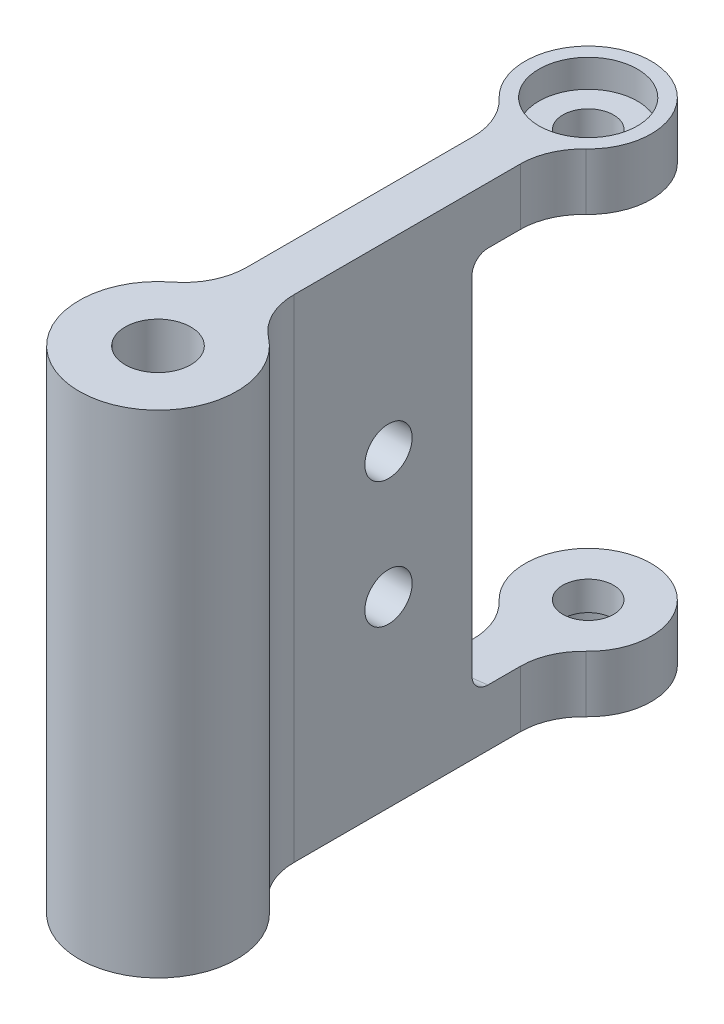
SolidWorks part; units mm, degrees
ref_plane "Front Plane" through (0, 0, 0) normal (0, 0, 1) x (1, 0, 0)
ref_plane "Top Plane" through (0, 0, 0) normal (0, 1, 0) x (1, 0, 0)
ref_plane "Right Plane" through (0, 0, 0) normal (1, 0, 0) x (0, 0, -1)
sketch "Sketch1" plane through (0, 0, 0) normal (0, 1, 0) x (1, 0, 0)
  line L3 (-2.3813, 37.4437) -> (-2.3813, 7.5719)
  line L5 (2.3813, 7.5719) -> (2.3812, 37.4437)
  arc A0 (-2.3813, 7.5719) -> (2.3813, 7.5719) centre (0, 0) ccw
  circle A1 centre (0, 0) radius 3.302
  arc A2 (2.3812, 37.4437) -> (-2.3813, 37.4437) centre (0, 43.3303) ccw
  point P5 (-1.3127, 7.8282)
  point P6 (0, 0)
  point P7 (6.35, 42.3895)
  point P10 (5.9087, -6.1989)
  point P11 (-3.0351, 7.3343)
  point P13 (0, -7.9375)
  point P14 (1.1462, -7.8533)
  point P15 (7.8032, -1.454)
  point P16 (7.7434, -1.7446)
  point P17 (7.5964, 2.3017)
  point P18 (-1.9476, 7.4216)
  point P19 (0.4871, 51.969)
  point P20 (7.8311, 49.325)
  point P21 (7.8311, 50.2543)
  point P22 (5.6114, 35.2031)
  point P23 (0, 0)
  dimension "D1" = 6.604
  dimension "D2" = 7.9375
  dimension "D6" = 43.3303
  dimension "D4" = 6.35
  dimension "D3" = 4.7625
extrude "Boss-Extrude1" add sketch "Sketch1" along normal mid plane 49.53
fillet "Fillet1" radius 6.35 4 edges at (-2.3813, 0, -37.4437) (-2.3813, 0, -7.5719) (2.3813, 0, -7.5719) (2.3812, 0, -37.4437)
sketch "Sketch4" plane through (0, 0, 0) normal (0, 1, 0) x (1, 0, 0)
  circle A0 centre (0, 43.3303) radius 14.2875
  arc A1 (4.3656, 38.719) -> (-4.3656, 38.719) centre (0, 43.3303) ccw construction
  arc A2 (4.3656, 38.719) -> (-4.3656, 38.719) centre (0, 43.3303) ccw
  dimension "D1" = 28.575
extrude "Cut-Extrude1" cut sketch "Sketch4" against normal mid plane 38.1 contours A0
hole_wizard "CBORE for #10 Button Head Cap Screw1" positions "Sketch5" profile "Sketch6" counterbore size "#10" standard "ANSI Inch"
sketch "Sketch5" plane through (0, 24.765, 0) normal (0, 1, 0) x (1, 0, 0)
  point P0 (0, 43.3303)
sketch "Sketch6" plane through (0, 24.765, -43.3303) normal (1, 0, 0) x (0, 0, 1)
  line L0 (0, 0) -> (0, 49.53)
  line L1 (0, 49.53) -> (2.5527, 49.53)
  line L3 (2.5527, 49.53) -> (2.5527, 2.794)
  line L4 (2.5527, 2.794) -> (4.9606, 2.794)
  line L5 (4.9606, 2.794) -> (4.9606, 0)
  line L7 (4.9606, 0) -> (0, 0)
  line L11 (0, -6.35) -> (0, 107.95) construction
  dimension "Thru Hole Dia." = 5.1054
  dimension "Thru Hole Depth" = 49.53
  dimension "C'Bore Dia." = 9.9212
  dimension "C'Bore Depth" = 2.794
mirror "Mirror1" about plane through (0, 0, 0) normal (0, 1, 0) of "CBORE for #10 Button Head Cap Screw1"
fillet "Fillet2" radius 1.5875 2 edges at (0, -19.05, -29.0428) (0, 19.05, -29.0428)
sketch "Sketch7" plane through (-2.3812, 0, 0) normal (-1, 0, 0) x (0, 0, 1)
  line L0 (-20.8342, -6.35) -> (-20.8342, 6.35)
  line L1 (-11.3092, -24.765) -> (-11.3092, 24.765) construction
  circle A0 centre (-20.8342, -6.35) radius 2.3813
  circle A1 centre (-20.8342, 6.35) radius 2.3813
  point P4 (-20.8342, 0)
  dimension "D2" = 4.7625
  dimension "D1" = 9.525
  dimension "D3" = 12.7
extrude "Cut-Extrude2" cut sketch "Sketch7" against normal through all
